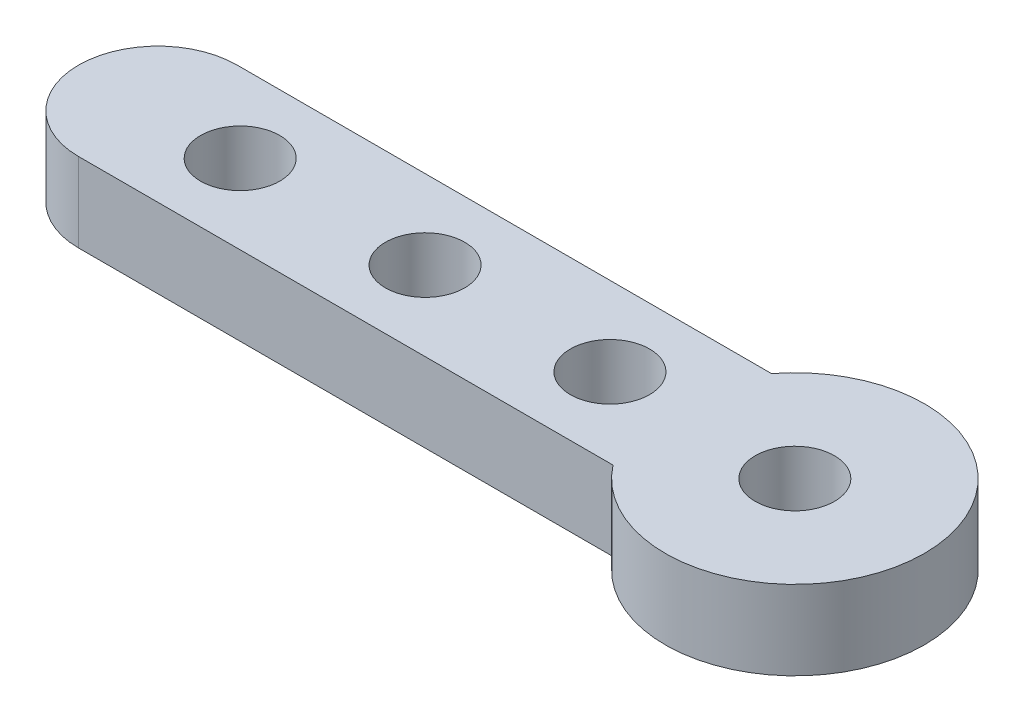
SolidWorks part; units mm, degrees
ref_plane "Front Plane" through (0, 0, 0) normal (0, 0, 1) x (1, 0, 0)
ref_plane "Top Plane" through (0, 0, 0) normal (0, 1, 0) x (1, 0, 0)
ref_plane "Right Plane" through (0, 0, 0) normal (1, 0, 0) x (0, 0, -1)
sketch "Sketch2" plane through (0, 0, 0) normal (0, 1, 0) x (1, 0, 0)
  line L0 (15, 6) -> (15, 0) construction
  line L1 (4.8839, 0) -> (25.1161, 0)
  line L3 (4.8839, 6) -> (25.1161, 6)
  arc A1 (25.1161, 6) -> (25.1161, 0) centre (29, 3) cw
  circle A2 centre (15, 3) radius 1.5
  circle A3 centre (8, 3) radius 1.5
  circle A4 centre (22, 3) radius 1.5
  circle A5 centre (29, 3) radius 1.5
  arc A6 (4.8839, 6) -> (4.8839, 0) centre (4.8839, 3) ccw
  dimension "D4" = 3
  dimension "D5" = 3
  dimension "D7" = 3
  dimension "D8" = 6
  dimension "D1" = 7
  dimension "D2" = 7
  dimension "D6" = 7
extrude "Boss-Extrude1" add sketch "Sketch2" along normal blind 3 contours A3 | L3 A1 L1 A6 | A2 | A4 | A5
